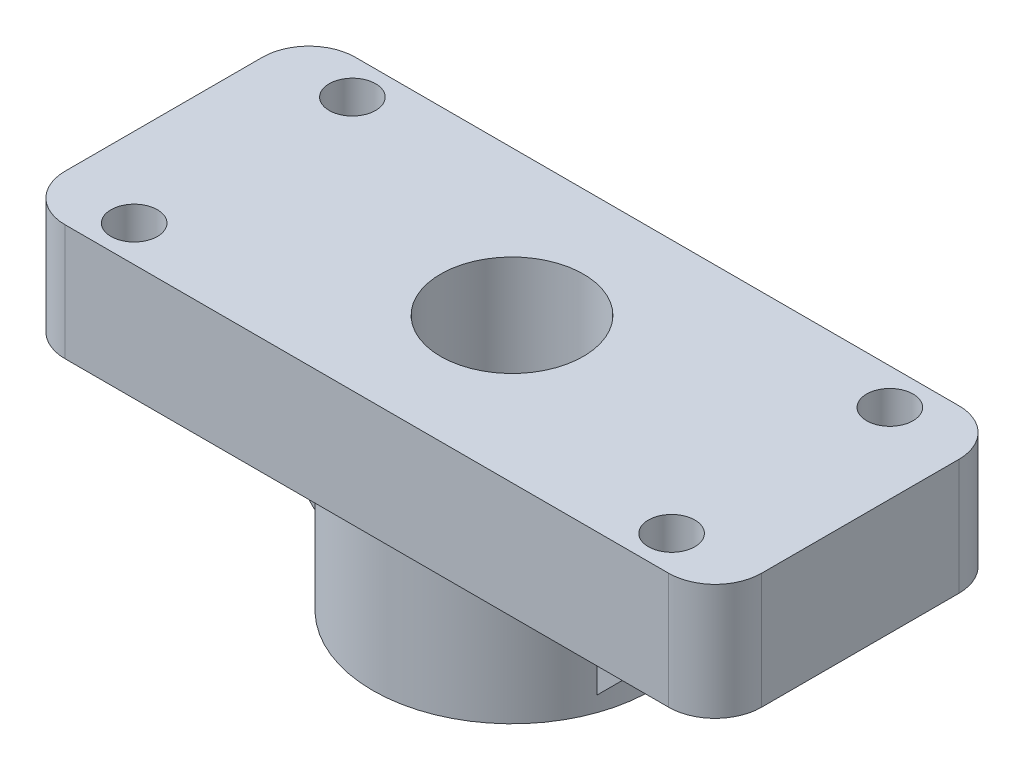
SolidWorks part; units mm, degrees
ref_plane "Front Plane" through (0, 0, 0) normal (0, 0, 1) x (1, 0, 0)
ref_plane "Top Plane" through (0, 0, 0) normal (0, 1, 0) x (1, 0, 0)
ref_plane "Right Plane" through (0, 0, 0) normal (1, 0, 0) x (0, 0, -1)
sketch "Sketch1" plane through (0, 0, 0) normal (0, 1, 0) x (1, 0, 0)
  line L1 (-30, 12.5) -> (30, 12.5)
  line L2 (-30, 12.5) -> (-30, -12.5)
  line L3 (-30, -12.5) -> (30, -12.5)
  line L4 (30, 12.5) -> (30, -12.5)
  point P4 (0, 12.5)
  point P6 (-30, 0)
  dimension "D1" = 25
  dimension "D2" = 60
extrude "Base" add sketch "Sketch1" along normal blind 10
sketch "Sketch2" plane through (0, 0, 0) normal (0, 0, 1) x (1, 0, 0)
  line L0 (0, 0) -> (0, -20.6179) construction
  line L1 (-6.15, 0) -> (-6.15, -7)
  line L2 (-30, 0) -> (30, 0) construction
  line L3 (-6.15, -7) -> (-5.4, -7)
  line L4 (-5.4, -7) -> (-5.4, -12)
  line L5 (-5.4, -12) -> (-12, -12)
  line L6 (-12, -12) -> (-12, 0)
  line L7 (-12, 0) -> (-6.15, 0)
  dimension "D1" = 12
  dimension "D2" = 6.15
  dimension "D3" = 5.4
  dimension "D4" = 12
  dimension "D5" = 7
revolve "Pen Catch" add sketch "Sketch2" angle 360 about L0
sketch "Sketch5" plane through (0, 10, 0) normal (0, 1, 0) x (1, 0, 0)
  circle A0 centre (0, 0) radius 6.15
  dimension "D1" = 12.3
extrude "Pen Hole" cut sketch "Sketch5" against normal up to next
sketch "Sketch4" plane through (0, 0, 0) normal (0, 0, 1) x (1, 0, 0)
  line L0 (-22, 0) -> (-10, 0)
  line L1 (-30, 0) -> (30, 0) construction
  line L2 (-10, 0) -> (-10, -12)
  line L3 (-10, -12) -> (-22, 0)
  line L4 (0, 0) -> (0, -27.3362) construction
  line L5 (-12, 0) -> (-12, -12) construction
  line L6 (10, -12) -> (22, 0)
  line L7 (10, 0) -> (10, -12)
  line L8 (22, 0) -> (10, 0)
  dimension "D1" = 45
  dimension "D2" = 10
  dimension "D3" = 12
extrude "Stab Fins" add sketch "Sketch4" along normal blind 4 and the other way blind 4
fillet "Base Dec" radius 4 4 edges at (-30, 5, -12.5) (30, 5, 12.5) (30, 5, -12.5) (-30, 5, 12.5)
sketch "Sketch8" plane through (0, 10, 0) normal (0, 1, 0) x (1, 0, 0)
  circle A0 centre (23.15, 9.4) radius 2
  circle A1 centre (23.15, -9.4) radius 2
  circle A2 centre (-23.15, 9.4) radius 2
  circle A3 centre (-23.15, -9.4) radius 2
  circle A4 centre (23.15, 9.4) radius 2 construction
  circle A5 centre (23.15, -9.4) radius 2 construction
  circle A6 centre (-23.15, -9.4) radius 2 construction
  circle A7 centre (-23.15, 9.4) radius 2 construction
extrude "Cut-Extrude2" cut sketch "Sketch8" against normal through all
chamfer "Chamfer1" distance 2 angle 45 1 edges at (0, -12, 5.4)
